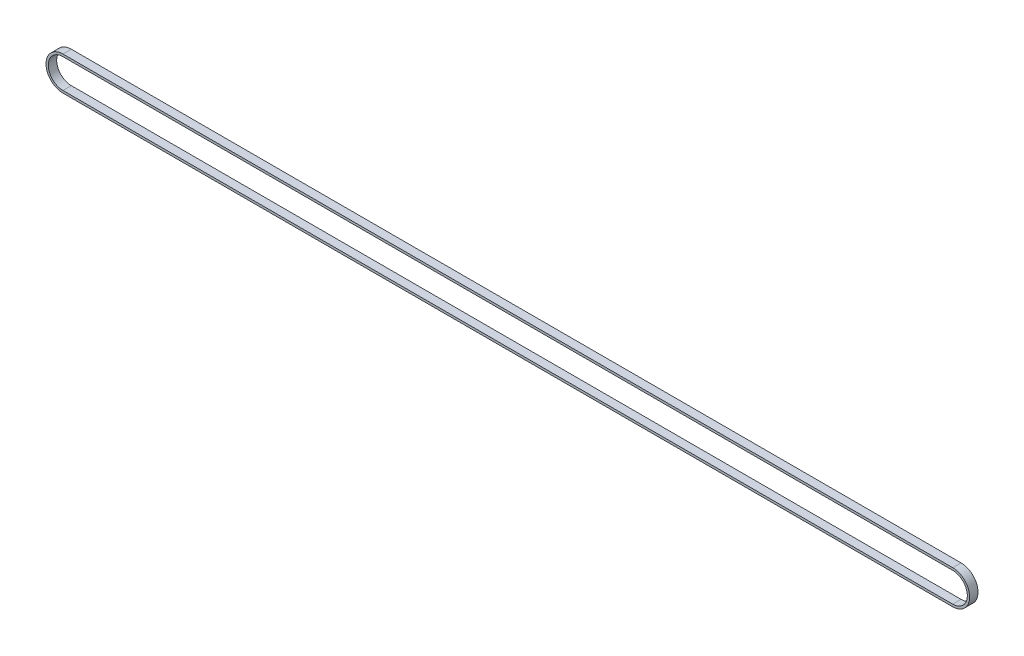
SolidWorks part; units mm, degrees
material "Rubber"
ref_plane "Front Plane" through (0, 0, 0) normal (0, 0, 1) x (1, 0, 0)
ref_plane "Top Plane" through (0, 0, 0) normal (0, 1, 0) x (1, 0, 0)
ref_plane "Right Plane" through (0, 0, 0) normal (1, 0, 0) x (0, 0, -1)
sketch "Sketch1" plane through (0, 0, 0) normal (0, 0, 1) x (1, 0, 0)
  line L0 (0, 0) -> (532, 0) construction
  line L1 (0, 8.75) -> (532, 8.75)
  line L2 (532, -8.75) -> (0, -8.75)
  arc A0 (0, 8.75) -> (0, -8.75) centre (0, 0) ccw
  arc A1 (532, -8.75) -> (532, 8.75) centre (532, 0) ccw
  dimension "D1" = 17.5
  dimension "D2" = 532
extrude "Extrude-Thin1" add sketch "Sketch1" along normal mid plane 5 thin thin type one direction wall 1.38
